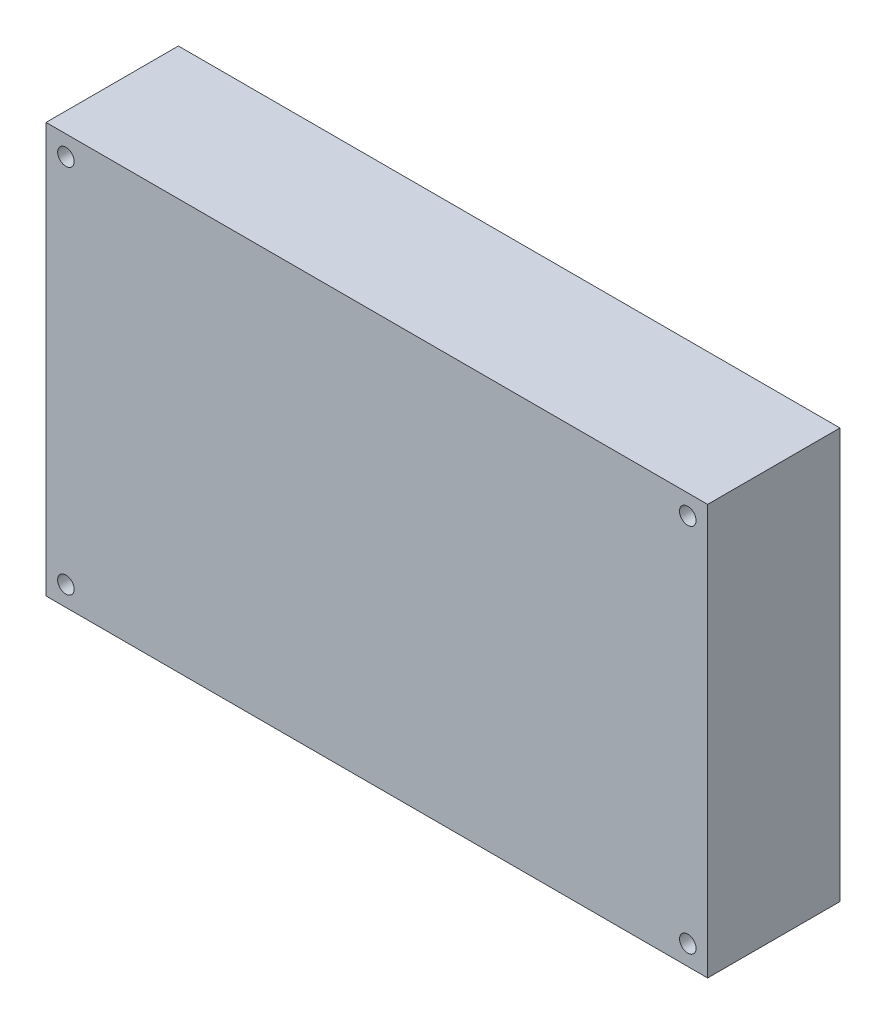
SolidWorks part; units mm, degrees
ref_plane "前视基准面" through (0, 0, 0) normal (0, 0, 1) x (1, 0, 0)
ref_plane "上视基准面" through (0, 0, 0) normal (0, 1, 0) x (1, 0, 0)
ref_plane "右视基准面" through (0, 0, 0) normal (1, 0, 0) x (0, 0, -1)
sketch "草图1" plane through (0, 0, 0) normal (0, 0, 1) x (1, 0, 0)
  line L1 (-50, -31) -> (50, -31)
  line L2 (-50, -31) -> (-50, 31)
  line L3 (-50, 31) -> (50, 31)
  line L4 (50, -31) -> (50, 31)
  line L5 (-50, -31) -> (50, 31) construction
  line L6 (-50, 31) -> (50, -31) construction
  point P0 (0, 0)
  dimension "D1" = 62
  dimension "D2" = 100
extrude "凸台-拉伸1" add sketch "草图1" along normal blind 20
hole_wizard "M3 螺纹孔1" positions "草图2" profile "草图3" tap size "M3" standard "GB" end condition through all
sketch "草图2" plane through (0, 0, 20) normal (0, 0, 1) x (1, 0, 0)
  line L0 (-68.208, 0) -> (75.1299, 0) construction
  line L2 (0, 37.4318) -> (0, -42.5435) construction
  point P0 (-47, 28)
  point P15 (-47, -28)
  point P16 (47, -28)
  point P17 (47, 28)
  dimension "D1" = 94
  dimension "D2" = 56
cosmetic thread "孔螺蚊线1" parameters "D2"=3
cosmetic thread "孔螺蚊线2" parameters "D2"=3
cosmetic thread "孔螺蚊线3" parameters "D2"=3
cosmetic thread "孔螺蚊线4" parameters "D2"=3
sketch "草图3" plane through (-47, 28, 20) normal (1, 0, 0) x (0, -1, 0)
  line L0 (0, 0) -> (0, 20)
  line L1 (0, 20) -> (1.25, 20)
  line L2 (1.25, 20) -> (1.25, 0)
  line L5 (1.25, 0) -> (0, 0)
  line L11 (0, -6.35) -> (0, 107.95) construction
  dimension "通孔螺纹孔钻头直径" = 2.5
  dimension "通孔螺纹孔钻头深度" = 20
